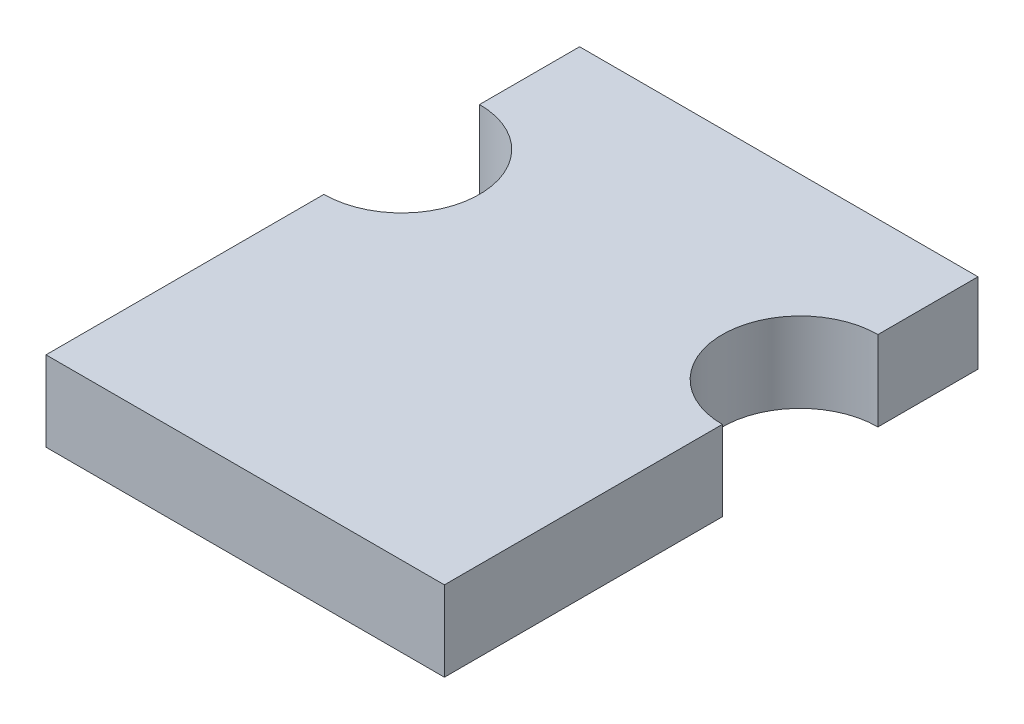
SolidWorks part; units mm, degrees
ref_plane "Alzado" through (0, 0, 0) normal (0, 0, 1) x (1, 0, 0)
ref_plane "Planta" through (0, 0, 0) normal (0, 1, 0) x (1, 0, 0)
ref_plane "Vista lateral" through (0, 0, 0) normal (1, 0, 0) x (0, 0, -1)
sketch "Croquis1" plane through (0, 0, 0) normal (0, 1, 0) x (1, 0, 0)
  line L0 (-4.48, 12) -> (-4.48, 0) construction
  line L1 (0, 0) -> (-8.96, 0)
  line L2 (0, 0) -> (0, 6.25)
  line L3 (0, 12) -> (-8.96, 12)
  line L4 (-8.96, 0) -> (-8.96, 6.25)
  line L5 (-8.96, 9.75) -> (-8.96, 12)
  line L6 (0, 9.75) -> (0, 12)
  arc A0 (-8.96, 6.25) -> (-8.96, 9.75) centre (-8.96, 8) ccw
  arc A1 (0, 6.25) -> (0, 9.75) centre (0, 8) cw
  dimension "D4" = 3.5
  dimension "D1" = 8.96
  dimension "D2" = 12
  dimension "D3" = 4
extrude "Saliente-Extruir1" add sketch "Croquis1" along normal blind 1.8
